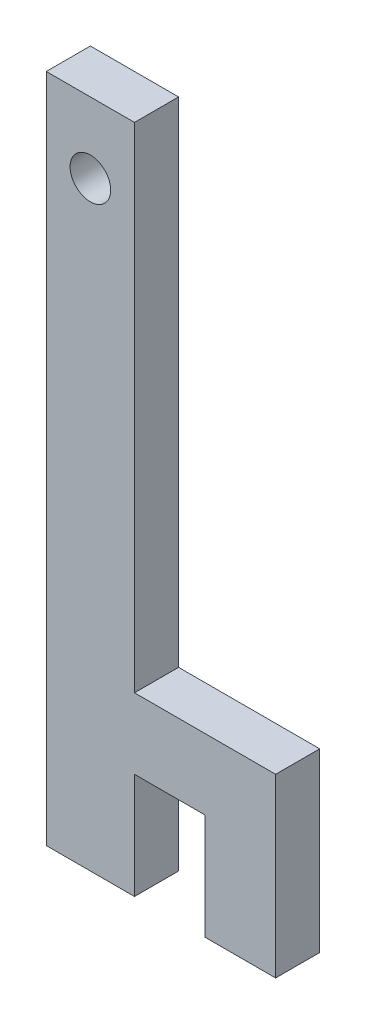
SolidWorks part; units mm, degrees
ref_plane "Front Plane" through (0, 0, 0) normal (0, 0, 1) x (1, 0, 0)
ref_plane "Top Plane" through (0, 0, 0) normal (0, 1, 0) x (1, 0, 0)
ref_plane "Right Plane" through (0, 0, 0) normal (1, 0, 0) x (0, 0, -1)
sketch "Sketch1" plane through (0, 0, 0) normal (0, 0, 1) x (1, 0, 0)
  line L1 (0, 0) -> (6.35, 0)
  line L2 (0, 0) -> (0, 48.26)
  line L3 (0, 48.26) -> (6.35, 48.26)
  line L4 (6.35, 0) -> (6.35, 48.26)
  dimension "D1" = 6.35
  dimension "D2" = 48.26
extrude "Boss-Extrude1" add sketch "Sketch1" along normal blind 3.175 contours L1 L4 L3 L2
sketch "Sketch3" plane through (0, 0, 3.175) normal (0, 0, 1) x (1, 0, 0)
  line L0 (3.175, 48.26) -> (3.175, 43.18)
  line L1 (0, 48.26) -> (6.35, 48.26) construction
  circle A0 centre (3.175, 43.18) radius 1.4605
  dimension "D2" = 2.921
  dimension "D1" = 5.08
extrude "Cut-Extrude2" cut sketch "Sketch3" against normal through all
sketch "Sketch5" plane through (0, 0, 0) normal (0, 0, -1) x (-1, 0, 0)
  line L10 (-6.35, 12.7) -> (-16.51, 12.7)
  line L11 (-6.35, 0) -> (-6.35, 48.26) construction
  line L12 (-16.51, 12.7) -> (-16.51, 0)
  line L13 (-16.51, 0) -> (-11.43, 0)
  line L14 (-11.43, 0) -> (-11.43, 7.62)
  line L15 (-11.43, 7.62) -> (-6.35, 7.62)
  line L16 (-6.35, 7.62) -> (-6.35, 12.7)
  dimension "D5" = 10.16
  dimension "D6" = 7.62
  dimension "D7" = 5.08
extrude "Boss-Extrude3" add sketch "Sketch5" against normal blind 3.175
